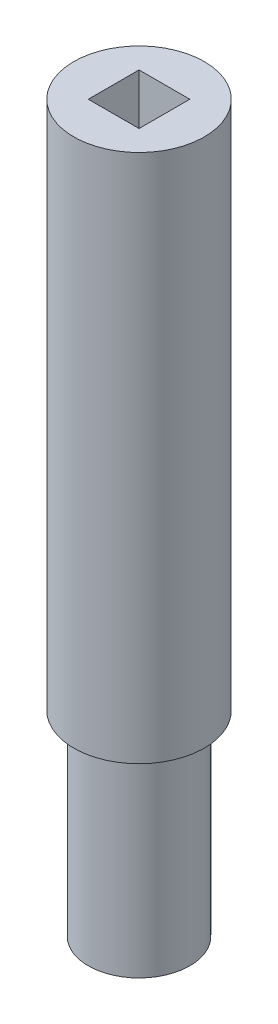
SolidWorks part; units mm, degrees
material "普通碳钢"
ref_plane "前视基准面" through (0, 0, 0) normal (0, 0, 1) x (1, 0, 0)
ref_plane "上视基准面" through (0, 0, 0) normal (0, 1, 0) x (1, 0, 0)
ref_plane "右视基准面" through (0, 0, 0) normal (1, 0, 0) x (0, 0, -1)
sketch "草图1" plane through (0, 0, 0) normal (0, 0, 1) x (1, 0, 0)
  line L0 (0, 0) -> (0, 100) construction
  line L1 (0, 0) -> (-7, 0)
  line L2 (-7, 0) -> (-7, 27)
  line L3 (0, 100) -> (-9, 100)
  line L4 (0, 100) -> (0, 0)
  line L5 (-7, 27) -> (-9, 27)
  line L6 (-9, 27) -> (-9, 100)
  dimension "D1" = 100
  dimension "D2" = 7
  dimension "D3" = 9
  dimension "D4" = 27
revolve "旋转1" add sketch "草图1" angle 360 about L0
sketch "草图2" plane through (0, 100, 0) normal (0, 1, 0) x (1, 0, 0)
  line L1 (-3.5, -3.5) -> (3.5, -3.5)
  line L2 (-3.5, -3.5) -> (-3.5, 3.5)
  line L3 (-3.5, 3.5) -> (3.5, 3.5)
  line L4 (3.5, -3.5) -> (3.5, 3.5)
  line L5 (-3.5, -3.5) -> (3.5, 3.5) construction
  line L6 (-3.5, 3.5) -> (3.5, -3.5) construction
  point P0 (0, 0)
  dimension "D1" = 7
ref_plane "基准面1" through (0, 0, 5.5) normal (0, 0, 1) x (1, 0, 0)
ref_plane "基准面2" through (0, 0, -7) normal (0, 0, -1) x (-1, 0, 0)
extrude "切除-拉伸1" cut sketch "草图2" against normal blind 35
sketch "草图4" plane through (0, 0, -7) normal (0, 0, -1) x (-1, 0, 0)
  line L0 (0, 4) -> (0, 22) construction
  line L1 (-2.5, 4) -> (-2.5, 22)
  line L2 (2.5, 4) -> (2.5, 22)
  arc A0 (-2.5, 4) -> (2.5, 4) centre (0, 4) ccw
  arc A1 (2.5, 22) -> (-2.5, 22) centre (0, 22) ccw
  point P3 (0, 13)
  dimension "D1" = 2.5
  dimension "D2" = 18
  dimension "D3" = 4
extrude "切除-拉伸2" cut sketch "草图4" against normal blind 3
equation "\"2。5\"=4.69247"
